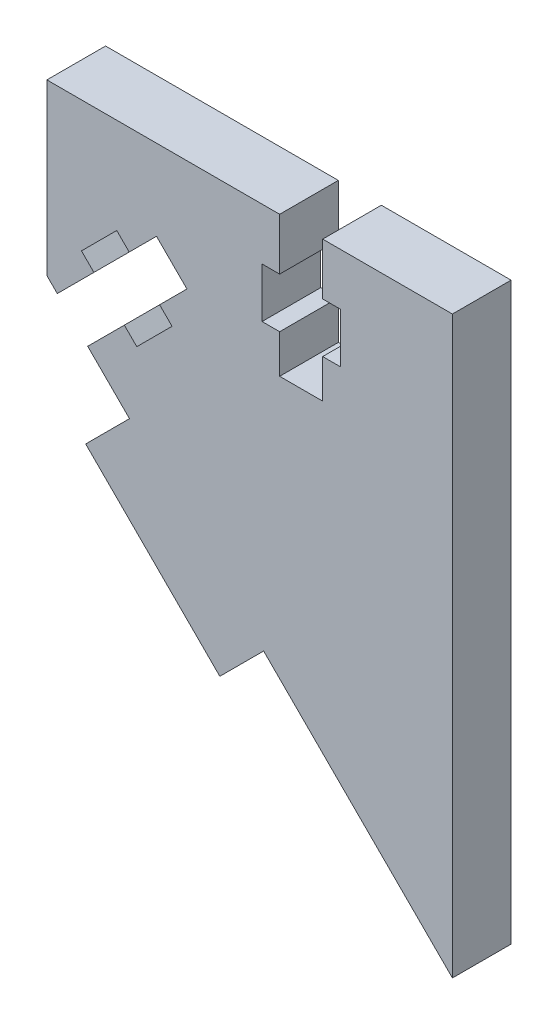
SolidWorks part; units mm, degrees
ref_plane "Plano frontal" through (0, 0, 0) normal (0, 0, 1) x (1, 0, 0)
ref_plane "Plano superior" through (0, 0, 0) normal (0, 1, 0) x (1, 0, 0)
ref_plane "Plano direito" through (0, 0, 0) normal (1, 0, 0) x (0, 0, -1)
sketch "Model" plane through (0, 0, 0) normal (0, 0, 1) x (1, 0, 0)
  line L0 (38.5627, 56.4595) -> (41.3558, 59.2526)
  line L1 (42.9468, 52.0754) -> (39.3405, 48.4692)
  line L2 (34.9565, 52.8532) -> (33.6837, 54.126)
  line L3 (38.5932, 41.7212) -> (34.3201, 45.9943)
  line L4 (38.5932, 41.7212) -> (34.1128, 37.2409)
  line L5 (34.1128, 37.2409) -> (47.8307, 23.523)
  line L6 (47.8307, 23.523) -> (52.311, 28.0034)
  line L7 (71.615, 67.4993) -> (71.615, 8.6993)
  line L8 (44.4671, 56.1413) -> (41.674, 53.3482)
  line L9 (37.2899, 57.7323) -> (38.5627, 56.4595)
  line L10 (58.3481, 67.4993) -> (58.3481, 62.1993)
  line L11 (58.3481, 62.1993) -> (60.1481, 62.1993)
  line L12 (39.3405, 48.4692) -> (38.0677, 49.742)
  line L13 (33.6837, 54.126) -> (37.2899, 57.7323)
  line L14 (38.0677, 49.742) -> (34.3201, 45.9943)
  line L15 (41.674, 53.3482) -> (42.9468, 52.0754)
  line L16 (41.3558, 59.2526) -> (44.4671, 56.1413)
  line L17 (31.2088, 49.1056) -> (34.9565, 52.8532)
  line L18 (60.1481, 62.1993) -> (60.1481, 57.0993)
  line L19 (60.1481, 57.0993) -> (58.3481, 57.0993)
  line L20 (58.3481, 57.0993) -> (58.3481, 53.1493)
  line L21 (71.615, 67.4993) -> (58.3481, 67.4993)
  line L22 (58.3481, 53.1493) -> (53.9481, 53.1493)
  line L23 (53.9481, 53.1493) -> (53.9481, 57.0993)
  line L24 (53.9481, 57.0993) -> (52.1481, 57.0993)
  line L25 (52.1481, 57.0993) -> (52.1481, 62.1993)
  line L26 (52.1481, 62.1993) -> (53.9481, 62.1993)
  line L27 (53.9481, 62.1993) -> (53.9481, 67.4993)
  line L28 (53.9481, 67.4993) -> (30.1481, 67.4993)
  line L29 (30.1481, 67.4993) -> (30.1481, 50.1662)
  line L30 (30.1481, 50.1662) -> (31.2088, 49.1056)
  line L31 (71.615, 8.6993) -> (52.311, 28.0034)
extrude "Ressalto-extrusão1" add sketch "Model" along normal blind 6
